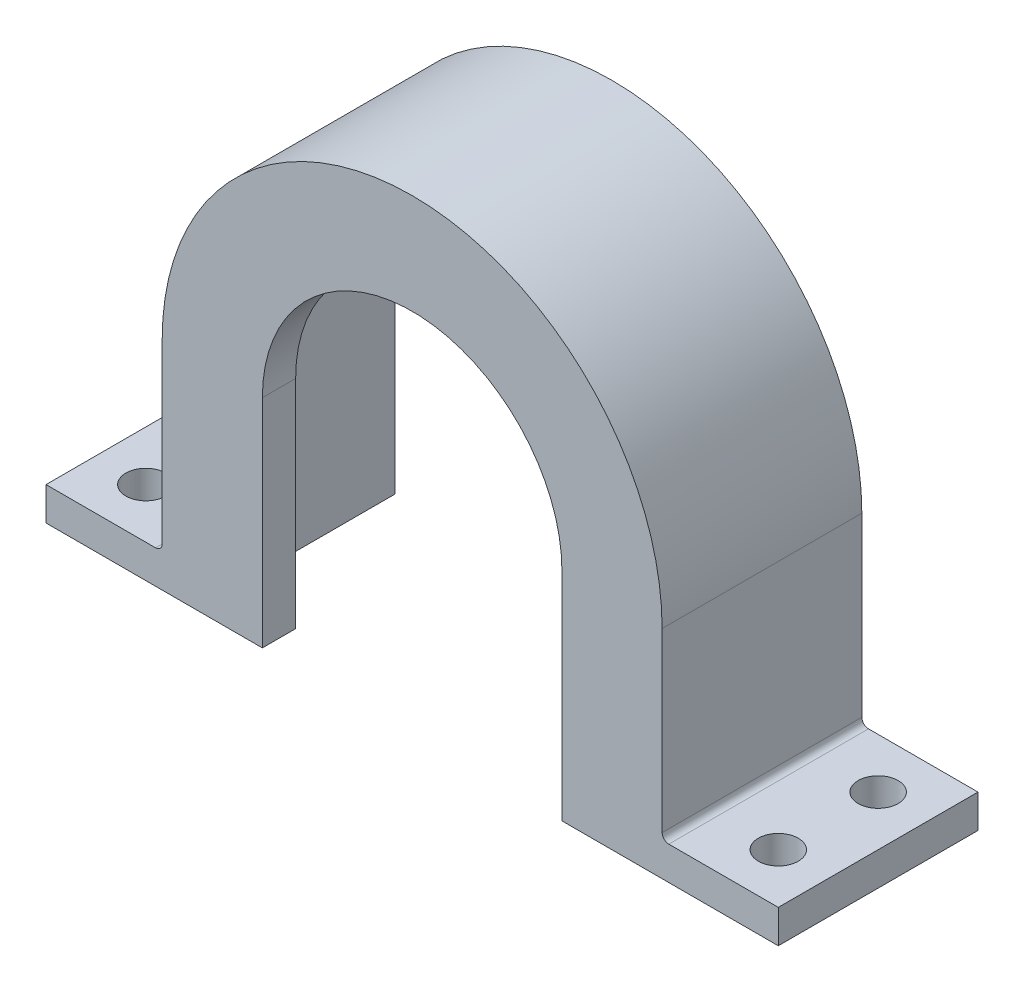
SolidWorks part; units mm, degrees
ref_plane "Plan de face" through (0, 0, 0) normal (0, 0, 1) x (1, 0, 0)
ref_plane "Plan de dessus" through (0, 0, 0) normal (0, 1, 0) x (1, 0, 0)
ref_plane "Plan de droite" through (0, 0, 0) normal (1, 0, 0) x (0, 0, -1)
sketch "Esquisse1" plane through (0, 0, 0) normal (0, 0, 1) x (1, 0, 0)
  line L0 (0, 104.9539) -> (0, -70.3398) construction
  line L1 (-55, 0) -> (55, 0)
  line L2 (37.55, 5) -> (37.55, 32.55)
  line L3 (-55, 0) -> (-55, 5)
  line L4 (-55, 5) -> (-37.55, 5)
  line L5 (-37.55, 5) -> (-37.55, 32.55)
  line L6 (55, 5) -> (37.55, 5)
  line L7 (55, 0) -> (55, 5)
  arc A0 (-37.55, 32.55) -> (37.55, 32.55) centre (0, 32.55) cw
  circle A1 centre (0, 32.55) radius 32.55 construction
  point P13 (0, 0)
  dimension "D2" = 5
  dimension "D1" = 32.55
  dimension "D3" = 110
  dimension "D4" = 5
extrude "Boss.-Extru.1" add sketch "Esquisse1" along normal blind 30
sketch "Esquisse2" plane through (0, 0, 0) normal (0, 0, -1) x (-1, 0, 0)
  line L0 (-22.5, 32.55) -> (-22.5, 0)
  line L1 (55, 0) -> (-55, 0) construction
  line L2 (-22.5, 0) -> (22.5, 0)
  line L3 (22.5, 0) -> (22.5, 32.55)
  line L4 (0, 57.9242) -> (0, -9.2925) construction
  arc A0 (-22.5, 32.55) -> (22.5, 32.55) centre (0, 32.55) cw
  arc A1 (37.55, 32.55) -> (-37.55, 32.55) centre (0, 32.55) ccw construction
  point P10 (0, 55.05)
  dimension "D1" = 22.5
extrude "Enlèv. mat.-Extru.1" cut sketch "Esquisse2" against normal through all
sketch "Esquisse3" plane through (0, 0, 0) normal (0, 0, -1) x (-1, 0, 0)
  line L0 (-32.55, 32.55) -> (-32.55, 0)
  line L1 (-22.5, 0) -> (-55, 0) construction
  line L2 (-32.55, 0) -> (32.55, 0)
  line L3 (55, 0) -> (22.5, 0) construction
  line L4 (32.55, 0) -> (32.55, 32.55)
  arc A0 (-32.55, 32.55) -> (32.55, 32.55) centre (0, 32.55) cw
  arc A1 (37.55, 32.55) -> (-37.55, 32.55) centre (0, 32.55) ccw construction
  dimension "D1" = 5
extrude "Enlèv. mat.-Extru.2" cut sketch "Esquisse3" against normal offset from surface (25 mm away) 5 up to face at (0, 17.5208, 30)
sketch "Esquisse4" plane through (0, 0, 0) normal (0, -1, 0) x (1, 0, 0)
  line L2 (55, 30) -> (55, 0) construction
  line L3 (-55, 15) -> (55, 15) construction
  line L4 (-55, 30) -> (-55, 0) construction
  line L5 (0, 0) -> (0, 30) construction
  line L6 (22.5, 30) -> (-22.5, 30) construction
  circle A0 centre (47.5, 7.5) radius 3
  circle A1 centre (-47.5, 7.5) radius 3
  circle A2 centre (47.5, 22.5) radius 3
  circle A3 centre (-47.5, 22.5) radius 3
  dimension "D3" = 6
  dimension "D1" = 95
  dimension "D2" = 15
extrude "Enlèv. mat.-Extru.3" cut sketch "Esquisse4" against normal up to surface (5 mm away) up to face at (46.275, 5, 15)
fillet "Congé1" radius 1 2 edges at (-37.55, 5, 15) (37.55, 5, 15)
